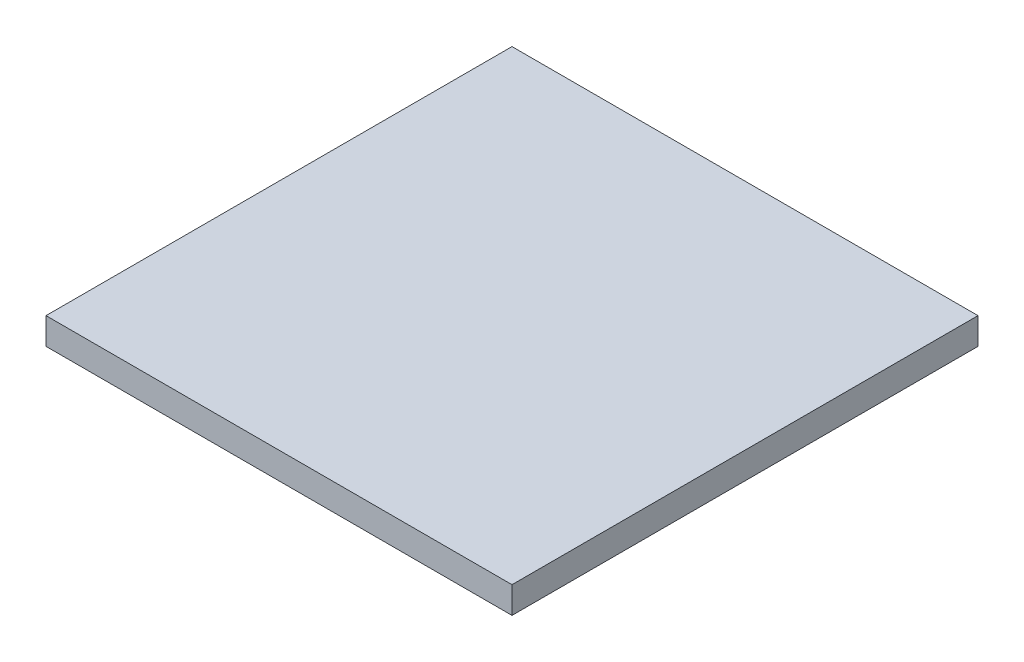
SolidWorks part; units mm, degrees
ref_plane "Front Plane" through (0, 0, 0) normal (0, 0, 1) x (1, 0, 0)
ref_plane "Top Plane" through (0, 0, 0) normal (0, 1, 0) x (1, 0, 0)
ref_plane "Right Plane" through (0, 0, 0) normal (1, 0, 0) x (0, 0, -1)
sketch "Sketch1" plane through (0, 0, 0) normal (0, 1, 0) x (1, 0, 0)
  line L0 (0, 0) -> (18.6879, 0) construction
  line L1 (0, 0) -> (0, -14.4281) construction
  line L3 (-3.5, 3.5) -> (3.5, 3.5)
  line L4 (-3.5, 3.5) -> (-3.5, -3.5)
  line L5 (-3.5, -3.5) -> (3.5, -3.5)
  line L6 (3.5, 3.5) -> (3.5, -3.5)
  dimension "D1" = 7
extrude "Boss-Extrude1" add sketch "Sketch1" along normal blind 0.4
